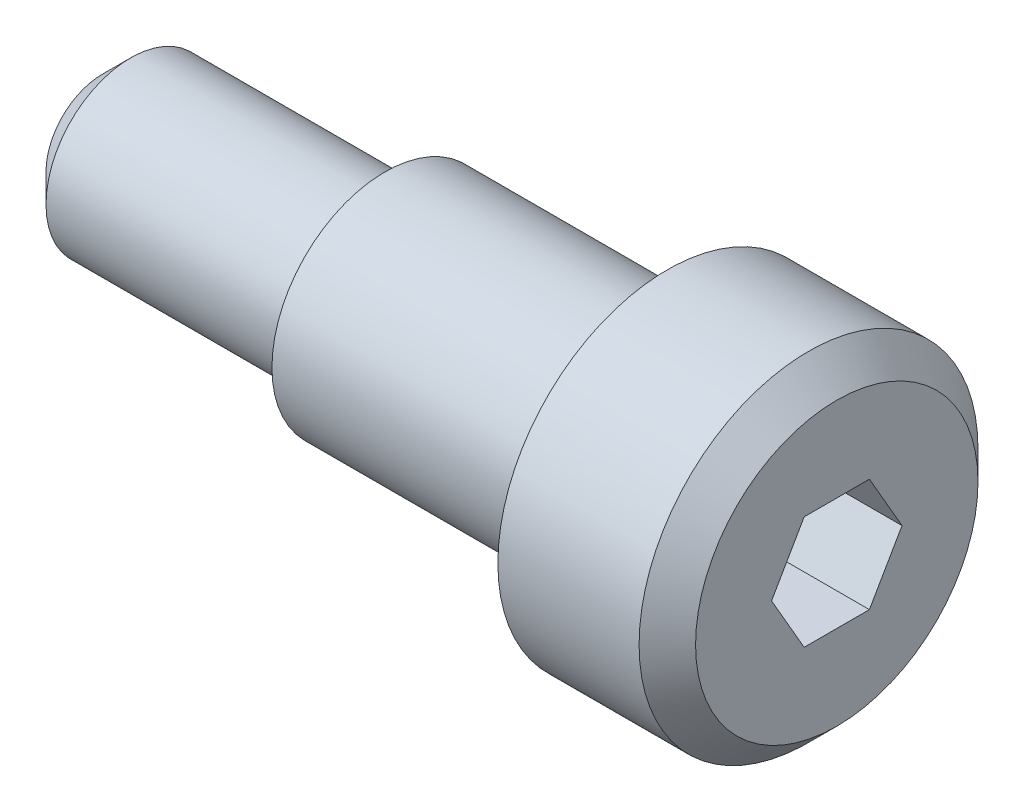
SolidWorks part; units mm, degrees
material "AISI Type 316L stainless steel"
ref_plane "Front Plane" through (0, 0, 0) normal (0, 0, 1) x (1, 0, 0)
ref_plane "Top Plane" through (0, 0, 0) normal (0, 1, 0) x (1, 0, 0)
ref_plane "Right Plane" through (0, 0, 0) normal (1, 0, 0) x (0, 0, -1)
sketch "Sketch1" plane through (0, 0, 0) normal (0, 0, 1) x (1, 0, 0)
  line L0 (0, 0) -> (13, 0)
  line L1 (13, 0) -> (13, 2.5)
  line L2 (12.5, 3) -> (10, 3)
  line L3 (10, 3) -> (10, 2)
  line L4 (10, 2) -> (5, 2)
  line L5 (5, 2) -> (5, 1.5)
  line L6 (5, 1.5) -> (0.5, 1.5)
  line L7 (0, 1) -> (0, 0)
  line L8 (0.5, 1.5) -> (0, 1)
  line L9 (13, 2.5) -> (12.5, 3)
  point P4 (13, 3)
  point P9 (0, 1.5)
  dimension "D1" = 5
  dimension "D2" = 1.5
  dimension "D3" = 5
  dimension "D4" = 2
  dimension "D5" = 3
  dimension "D6" = 3
revolve "Revolve1" add sketch "Sketch1" angle 360 about L0
sketch "Sketch2" plane through (13, 0, 0) normal (1, 0, 0) x (0, 0, -1)
  line L1 (1.1547, 0) -> (0.5774, 1)
  line L2 (0.5774, 1) -> (-0.5774, 1)
  line L3 (-0.5774, 1) -> (-1.1547, 0)
  line L4 (-1.1547, 0) -> (-0.5774, -1)
  line L5 (-0.5774, -1) -> (0.5774, -1)
  line L6 (0.5774, -1) -> (1.1547, 0)
  circle A0 centre (0, 0) radius 1 construction
  dimension "D1" = 2
extrude "Cut-Extrude1" cut sketch "Sketch2" against normal blind 4
